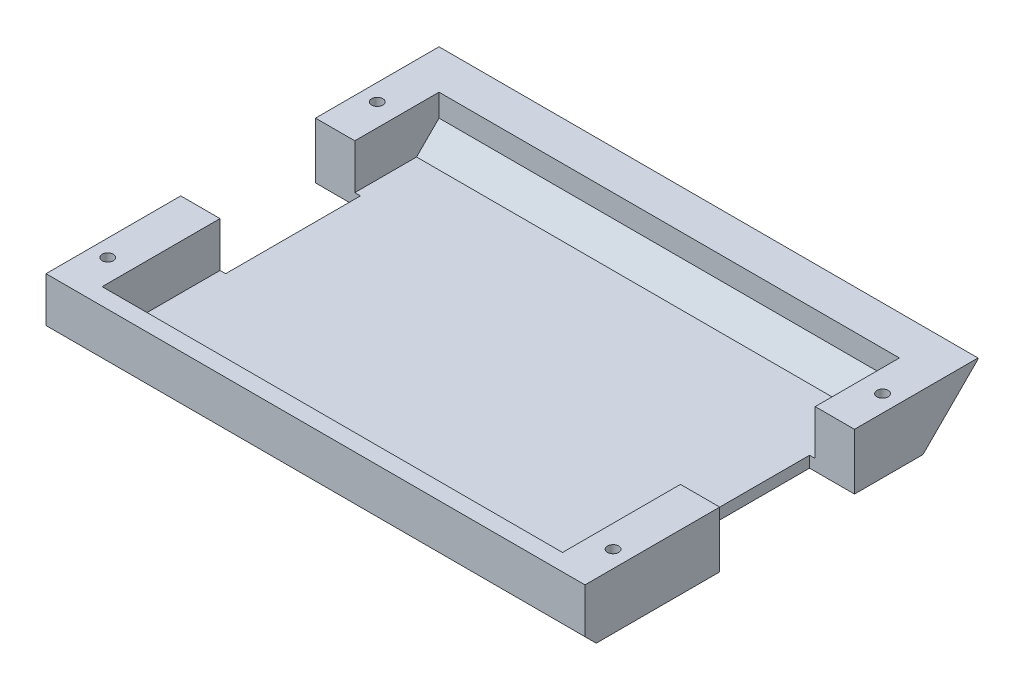
SolidWorks part; units mm, degrees
ref_plane "Front" through (0, 0, 0) normal (0, 0, 1) x (1, 0, 0)
ref_plane "Top" through (0, 0, 0) normal (0, 1, 0) x (1, 0, 0)
ref_plane "Right" through (0, 0, 0) normal (1, 0, 0) x (0, 0, -1)
sketch "草图1" plane through (0, 0, 0) normal (0, 1, 0) x (1, 0, 0)
  line L1 (24, -17.5) -> (-24, -17.5)
  line L2 (24, -17.5) -> (24, 17.5)
  line L3 (24, 17.5) -> (-24, 17.5)
  line L4 (-24, -17.5) -> (-24, 17.5)
  line L5 (24, -17.5) -> (-24, 17.5) construction
  line L6 (24, 17.5) -> (-24, -17.5) construction
  point P0 (0, 0)
  dimension "D1" = 48
  dimension "D2" = 35
extrude "凸台-拉伸1" add sketch "草图1" along normal blind 5
sketch "草图2" plane through (0, 5, 0) normal (0, 1, 0) x (1, 0, 0)
  line L1 (20.5, -16) -> (-20.5, -16)
  line L2 (20.5, -16) -> (20.5, 14)
  line L3 (20.5, 14) -> (-20.5, 14)
  line L4 (-20.5, -16) -> (-20.5, 14)
  line L5 (20.5, -16) -> (-20.5, 14) construction
  line L6 (20.5, 14) -> (-20.5, -16) construction
  line L7 (0, 0) -> (0, 31.8577) construction
  line L8 (24, 17.5) -> (-24, 17.5) construction
  point P0 (0, -1)
  dimension "D1" = 41
  dimension "D2" = 30
  dimension "D4" = 3.5
extrude "切除-拉伸1" cut sketch "草图2" against normal blind 4
sketch "草图3" plane through (0, 5, 0) normal (0, 1, 0) x (1, 0, 0)
  line L0 (0, 43.52) -> (0, -25.3766) construction
  line L2 (24, 17.5) -> (-24, 17.5) construction
  circle A0 centre (-22.5, 10.5) radius 0.5
  circle A5 centre (-22.5, -13.5) radius 0.5
  circle A6 centre (22.5, -13.5) radius 0.5
  circle A7 centre (22.5, 10.5) radius 0.5
  dimension "D1" = 1
  dimension "D2" = 24
  dimension "D3" = 7
extrude "切除-拉伸2" cut sketch "草图3" against normal through all
sketch "草图4" plane through (0, 0, 0) normal (0, -1, 0) x (1, 0, 0)
  circle A0 centre (-22.5, -10.5) radius 1
  circle A2 centre (-22.5, 13.5) radius 1
  circle A7 centre (22.5, 13.5) radius 1
  circle A8 centre (22.5, 13.5) radius 0.5 construction
  circle A9 centre (22.5, -10.5) radius 1
  circle A10 centre (22.5, -10.5) radius 0.5 construction
  circle A11 centre (-22.5, 13.5) radius 0.5 construction
  dimension "D1" = 2
  dimension "D3" = 2
extrude "切除-拉伸5" cut sketch "草图4" against normal blind 4
sketch "草图5" plane through (0, 5, 0) normal (0, 1, 0) x (1, 0, 0)
  line L0 (-24, 17.5) -> (-24, -17.5) construction
  line L1 (-20, -5.5) -> (-24, -5.5)
  line L2 (-20, -5.5) -> (-20, 6.5)
  line L3 (-20, 6.5) -> (-24, 6.5)
  line L4 (-24, -5.5) -> (-24, 6.5)
  line L5 (-20, -5.5) -> (-24, 6.5) construction
  line L6 (-20, 6.5) -> (-24, -5.5) construction
  line L8 (0, 8.1784) -> (0, -24.8927) construction
  line L9 (20, 6.5) -> (24, -5.5) construction
  line L10 (20, -5.5) -> (24, 6.5) construction
  line L21 (-24, -17.5) -> (24, -17.5) construction
  line L22 (24, -5.5) -> (24, 6.5)
  line L23 (20, 6.5) -> (24, 6.5)
  line L24 (20, -5.5) -> (20, 6.5)
  line L25 (20, -5.5) -> (24, -5.5)
  point P0 (-22, 0.5)
  point P14 (22, 0.5)
  dimension "D1" = 18
  dimension "D2" = 12
  dimension "D3" = 4
extrude "切除-拉伸4" cut sketch "草图5" against normal through all
chamfer "倒角2" distance 4.9 angle 45 1 edges at (0, 0, -17.5)
chamfer "倒角3" distance 1 angle 45 1 edges at (0, 0, 17.5)
chamfer "倒角6" distance 2 angle 45 1 edges at (0, 1, -14)
